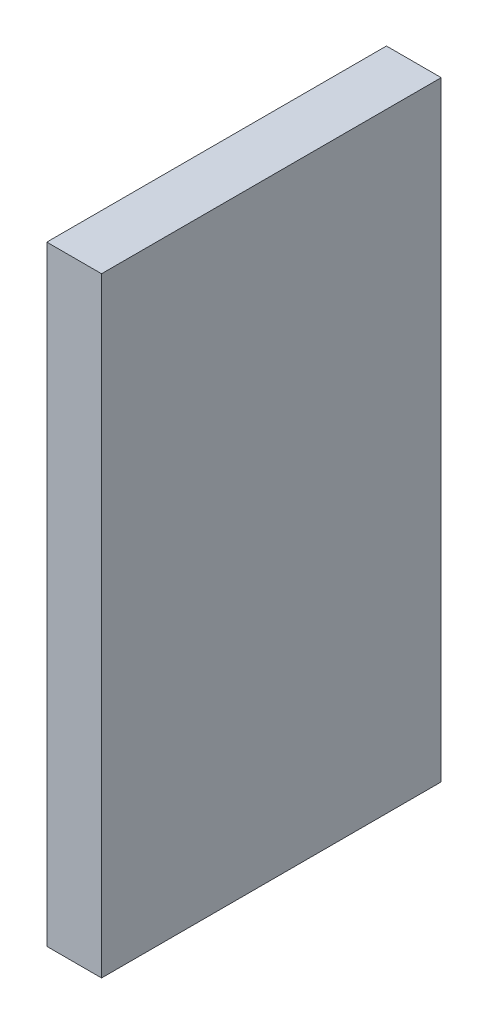
SolidWorks part; units mm, degrees
ref_plane "Alzado" through (0, 0, 0) normal (0, 0, 1) x (1, 0, 0)
ref_plane "Planta" through (0, 0, 0) normal (0, 1, 0) x (1, 0, 0)
ref_plane "Vista lateral" through (0, 0, 0) normal (1, 0, 0) x (0, 0, -1)
sketch "Croquis1" plane through (0, 0, 0) normal (1, 0, 0) x (0, 0, -1)
  line L0 (-25.8724, 8.7452) -> (-25.8724, -24.6548)
  line L1 (-25.8724, -24.6548) -> (-7.2724, -24.6548)
  line L2 (-7.2724, -24.6548) -> (-7.2724, 8.7452)
  line L3 (-7.2724, 8.7452) -> (-25.8724, 8.7452)
extrude "Saliente-Extruir1" add sketch "Croquis1" along normal blind 3
